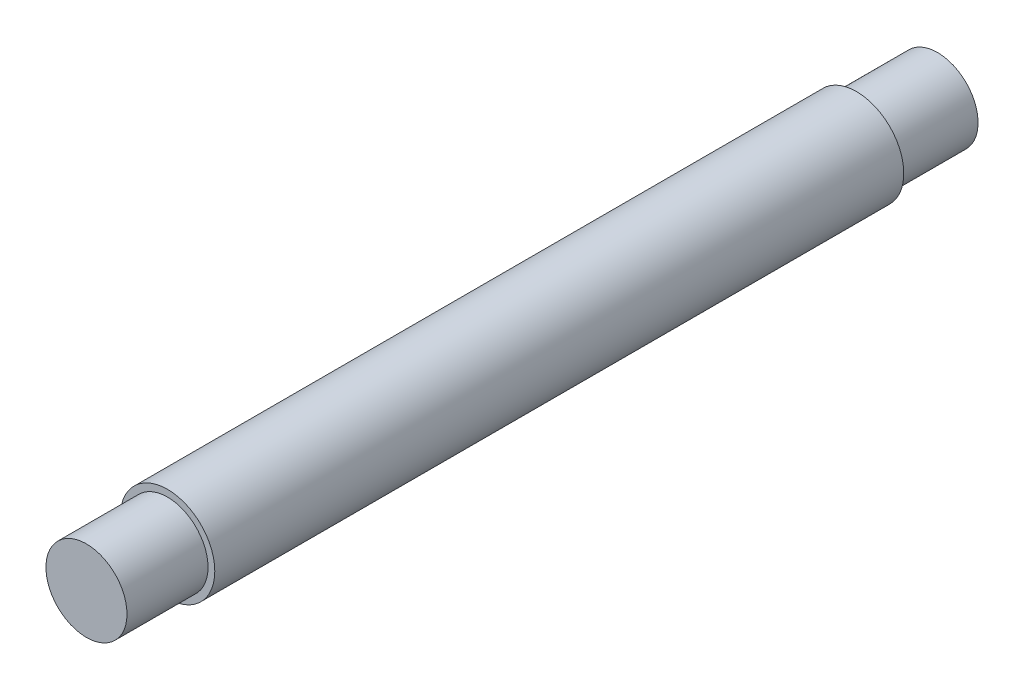
SolidWorks part; units mm, degrees
material "炭素鋼(鋳造)"
ref_plane "正面" through (0, 0, 0) normal (0, 0, 1) x (1, 0, 0)
ref_plane "平面" through (0, 0, 0) normal (0, 1, 0) x (1, 0, 0)
ref_plane "右側面" through (0, 0, 0) normal (1, 0, 0) x (0, 0, -1)
sketch "ｽｹｯﾁ1" plane through (0, 0, 0) normal (0, 0, 1) x (1, 0, 0)
  circle A0 centre (0, 0) radius 3.5
  dimension "D1" = 7
extrude "ﾎﾞｽ - 押し出し1" add sketch "ｽｹｯﾁ1" along normal blind 63
sketch "ｽｹｯﾁ2" plane through (0, 0, 63) normal (0, 0, 1) x (1, 0, 0)
  circle A0 centre (0, 0) radius 3
  circle A1 centre (0, 0) radius 5.2499
  dimension "D1" = 6
extrude "ｶｯﾄ - 押し出し1" cut sketch "ｽｹｯﾁ2" against normal blind 6
sketch "ｽｹｯﾁ3" plane through (0, 0, 0) normal (0, 0, -1) x (-1, 0, 0)
  circle A0 centre (0, 0) radius 3
  circle A1 centre (0, 0) radius 5.9607
  dimension "D1" = 6
extrude "ｶｯﾄ - 押し出し2" cut sketch "ｽｹｯﾁ3" against normal blind 6 contours A1 | A0
